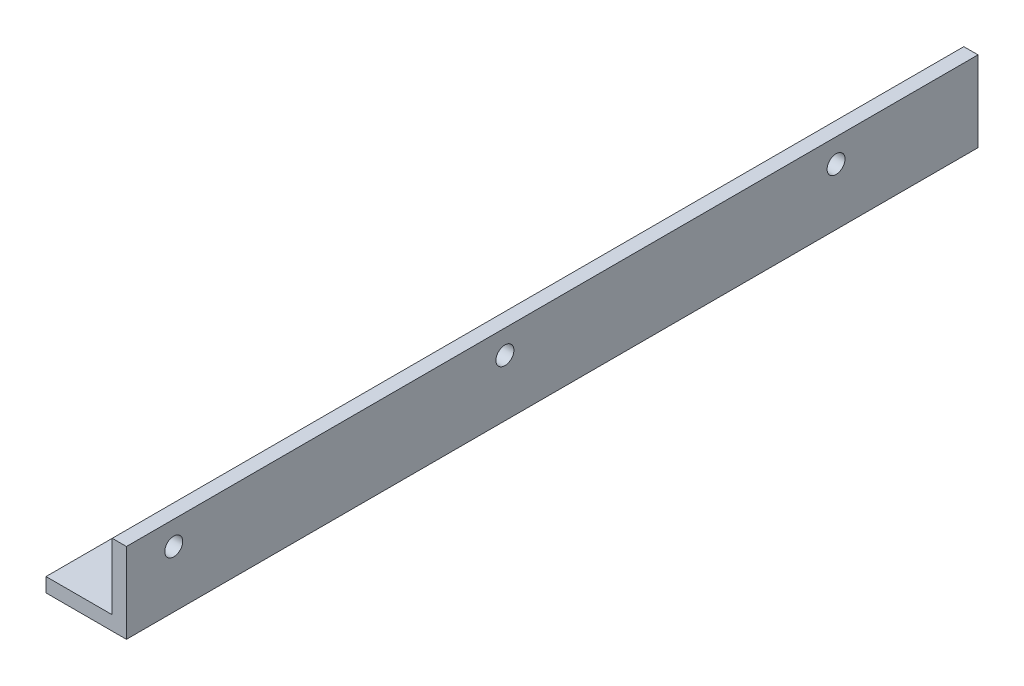
SolidWorks part; units mm, degrees
ref_plane "Front Plane" through (0, 0, 0) normal (0, 0, 1) x (1, 0, 0)
ref_plane "Top Plane" through (0, 0, 0) normal (0, 1, 0) x (1, 0, 0)
ref_plane "Right Plane" through (0, 0, 0) normal (1, 0, 0) x (0, 0, -1)
sketch "Sketch1" plane through (0, 0, 0) normal (0, 0, 1) x (1, 0, 0)
  line L0 (0, 0) -> (0, 17)
  line L1 (0, 17) -> (-3, 17)
  line L2 (-3, 17) -> (-3, 3)
  line L3 (-3, 3) -> (-17, 3)
  line L4 (-17, 3) -> (-17, 0)
  line L6 (-17, 0) -> (0, 0)
  point P4 (0, 0)
  dimension "D2" = 17
  dimension "D3" = 17
  dimension "D4" = 3
  dimension "D5" = 3
extrude "Boss-Extrude1" add sketch "Sketch1" along normal blind 180
sketch "Sketch2" plane through (-3, 0, 0) normal (-1, 0, 0) x (0, 0, 1)
  line L0 (0, 12) -> (180, 12) construction
  line L1 (0, 17) -> (0, 3) construction
  line L4 (180, 17) -> (0, 17) construction
  point P6 (30, 12)
  point P7 (100, 12)
  point P8 (170, 12)
  point P9 (0, 0)
  dimension "D1" = 140
  dimension "D2" = 70
  dimension "D3" = 30
  dimension "D4" = 5
hole_wizard "#6 Clearance Hole1" positions "Sketch3" profile "Sketch5" hole size "#6" standard "ANSI Inch" end condition through all
sketch "Sketch3" plane through (-3, 0, 0) normal (-1, 0, 0) x (0, 0, 1)
  point P0 (30, 12)
  point P3 (100, 12)
  point P6 (170, 12)
sketch "Sketch5" plane through (-3, 12, 30) normal (0, 1, 0) x (0, 0, 1)
  line L0 (0, 0) -> (0, 3)
  line L1 (0, 3) -> (1.8986, 3)
  line L2 (1.8986, 3) -> (1.8986, 0)
  line L5 (1.8986, 0) -> (0, 0)
  line L11 (0, -6.35) -> (0, 107.95) construction
  dimension "Thru Hole Dia." = 3.7973
  dimension "Thru Hole Depth" = 3
sketch "Sketch6" plane through (0, 3, 0) normal (0, 1, 0) x (1, 0, 0)
  line L0 (-12, 0) -> (-12, -180) construction
  line L1 (-3, 0) -> (-17, 0) construction
  line L3 (-17, -180) -> (-17, 0) construction
  point P6 (-12, -20)
  point P7 (-12, -90)
  point P8 (-12, -160)
  dimension "D1" = 20
  dimension "D2" = 140
  dimension "D3" = 70
  dimension "D4" = 5
hole_wizard "#6 Clearance Hole2" positions "Sketch7" profile "Sketch8" hole size "#6" standard "ANSI Inch" end condition through all
sketch "Sketch7" plane through (0, 3, 0) normal (0, 1, 0) x (1, 0, 0)
  point P0 (-12, -20)
  point P3 (-12, -90)
  point P6 (-12, -160)
sketch "Sketch8" plane through (-12, 3, 20) normal (1, 0, 0) x (0, 0, 1)
  line L0 (0, 0) -> (0, 3)
  line L1 (0, 3) -> (1.8986, 3)
  line L2 (1.8986, 3) -> (1.8986, 0)
  line L5 (1.8986, 0) -> (0, 0)
  line L11 (0, -6.35) -> (0, 107.95) construction
  dimension "Thru Hole Dia." = 3.7973
  dimension "Thru Hole Depth" = 3
